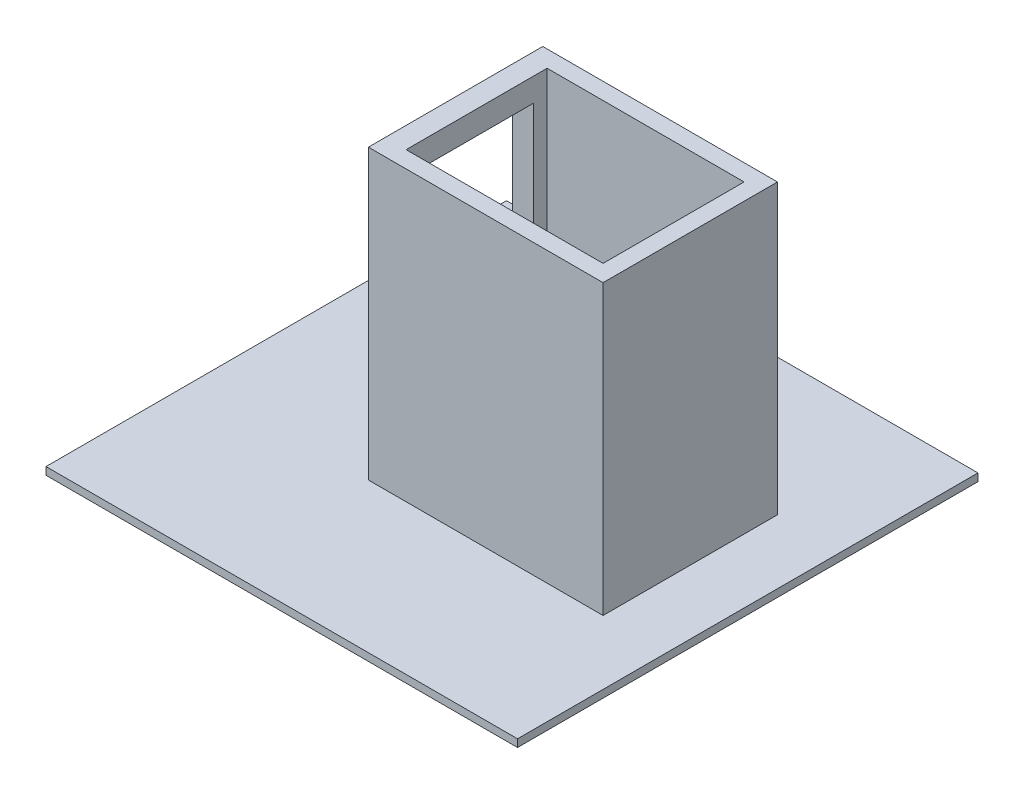
SolidWorks part; units mm, degrees
ref_plane "Front Plane" through (0, 0, 0) normal (0, 0, 1) x (1, 0, 0)
ref_plane "Top Plane" through (0, 0, 0) normal (0, 1, 0) x (1, 0, 0)
ref_plane "Right Plane" through (0, 0, 0) normal (1, 0, 0) x (0, 0, -1)
sketch "Sketch3" plane through (0, 0, 0) normal (0, 1, 0) x (1, 0, 0)
  line L0 (0, 0) -> (1436.8388, 0)
  line L1 (1436.8388, -110) -> (138.6234, -110)
  line L2 (138.6234, -110) -> (138.6234, -1039.471)
  line L3 (138.6234, -1039.471) -> (1436.8388, -1039.471)
  line L4 (1436.8388, 0) -> (1436.8388, -110)
  line L5 (0, 0) -> (0, -1149.471)
  line L9 (0, -1149.471) -> (1436.8388, -1149.471)
  line L12 (1436.8388, -1149.471) -> (1436.8388, -1039.471)
  dimension "D1" = 110
  dimension "D2" = 110
extrude "Boss-Extrude2" add sketch "Sketch3" along normal blind 1900 contours L0 L4 L1 L2 L3 L12 L9 L5
sketch "Sketch6" plane through (0, 0, 0) normal (-1, 0, 0) x (0, 0, 1)
  line L0 (0, 1900) -> (1149.471, 1900) construction
  line L2 (200, 1900) -> (917.8008, 1900) construction
  line L4 (200, -4.942) -> (917.8008, -4.942)
  line L6 (200, 1745.3877) -> (917.8008, 1745.3877)
  line L7 (200, -4.942) -> (200, 1745.3877)
  line L8 (917.8008, 1745.3877) -> (917.8008, -4.942)
extrude "Cut-Extrude1" cut sketch "Sketch6" against normal blind 1900
sketch "Sketch7" plane through (0, 0, 0) normal (0, -1, 0) x (-1, 0, 0)
  line L1 (1139.2719, 899.9867) -> (-1968.6383, 899.9867)
  line L2 (1139.2719, 899.9867) -> (1139.2719, -2135.1533)
  line L3 (1139.2719, -2135.1533) -> (-1968.6383, -2135.1533)
  line L4 (-1968.6383, 899.9867) -> (-1968.6383, -2135.1533)
extrude "Boss-Extrude3" add sketch "Sketch7" along normal blind 50
sketch "Sketch9" plane through (1436.8388, 0, 0) normal (1, 0, 0) x (0, 0, -1)
  line L1 (-1149.471, 1900) -> (0, 1900)
  line L2 (-1149.471, 1900) -> (-1149.471, 0)
  line L3 (-1149.471, 0) -> (0, 0)
  line L4 (0, 1900) -> (0, 0)
extrude "Boss-Extrude4" add sketch "Sketch9" along normal blind 110
